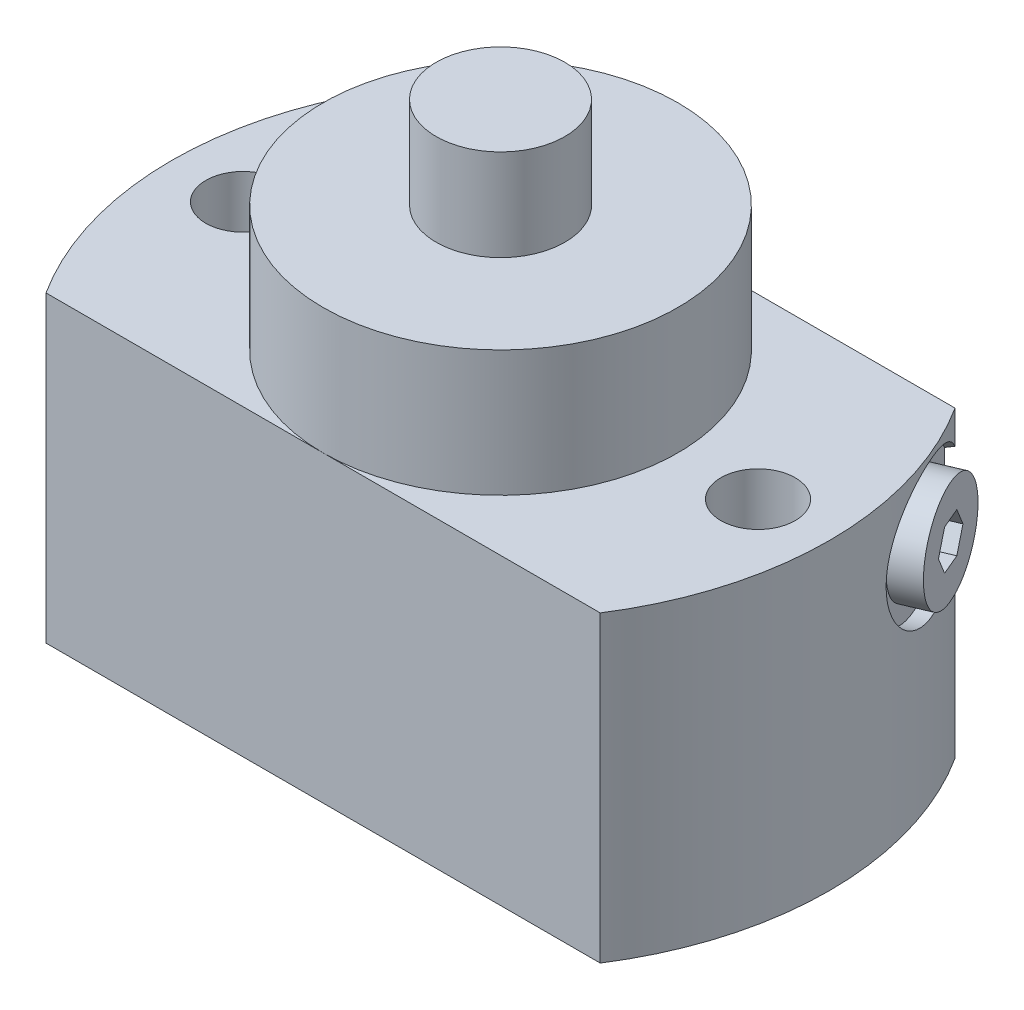
SolidWorks part; units mm, degrees
material "Alloy Steel"
ref_plane "Front Plane" through (0, 0, 0) normal (0, 0, 1) x (1, 0, 0)
ref_plane "Top Plane" through (0, 0, 0) normal (0, 1, 0) x (1, 0, 0)
ref_plane "Right Plane" through (0, 0, 0) normal (1, 0, 0) x (0, 0, -1)
sketch "Sketch1" plane through (0, 0, 0) normal (0, 1, 0) x (1, 0, 0)
  line L0 (-48.4278, 31) -> (48.4278, 31)
  line L1 (0, 0) -> (70.7148, 0) construction
  line L2 (-48.4278, -31) -> (48.4278, -31)
  arc A0 (-48.4278, 31) -> (-48.4278, -31) centre (0, 0) ccw
  arc A1 (48.4278, -31) -> (48.4278, 31) centre (0, 0) ccw
  dimension "D1" = 57.5
  dimension "D2" = 62
extrude "Extrude1" add sketch "Sketch1" along normal blind 53
sketch "Sketch2" plane through (0, 0, 0) normal (0, 0, 1) x (1, 0, 0)
  line L0 (0, 0) -> (0, 90.1953) construction
  line L1 (0, 91) -> (-11.25, 91)
  line L2 (-11.25, 91) -> (-11.25, 75)
  line L3 (-11.25, 75) -> (-31, 75)
  line L6 (-31, 75) -> (-31, 53)
  line L7 (-48.4278, 53) -> (48.4278, 53) construction
  line L8 (-31, 53) -> (0, 53)
  line L9 (0, 53) -> (0, 91)
  line L10 (-48.4278, 0) -> (48.4278, 0) construction
  point P8 (-32.8839, 75)
  dimension "D1" = 22.5
  dimension "D2" = 16
  dimension "D3" = 75
  dimension "D6" = 62
revolve "Revolve1" add sketch "Sketch2" angle 360 about L0
hole_wizard "Hole1" positions "Sketch4" profile "Sketch3" legacy end condition up to next
sketch "Sketch4" plane through (0, 53, 0) normal (0, 1, 0) x (-1, 0, 0)
  line L0 (0, 0) -> (0, 47.5777) construction
  point P0 (45, 0)
  point P7 (-45, 0)
  dimension "D1" = 90
sketch "Sketch3" plane through (-45, 53, 0) normal (1, 0, 0) x (0, 0, 1)
  line L0 (0, 0) -> (0, 53)
  line L1 (0, 53) -> (6.5, 53)
  line L2 (6.5, 53) -> (6.5, 0)
  line L3 (6.5, 0) -> (0, 0)
  line L4 (0, 110) -> (0, -10) construction
  dimension "Diameter" = 13
  dimension "Depth" = 53
sketch "Sketch5" plane through (0, 0, 0) normal (0, -1, 0) x (1, 0, 0)
  circle A0 centre (0, 0) radius 4
  dimension "D1" = 8
extrude "Cut-Extrude1" cut sketch "Sketch5" against normal blind 4
sketch "Sketch6" plane through (0, 0, 0) normal (0, -1, 0) x (1, 0, 0)
  circle A0 centre (35, -15) radius 5.5
  dimension "D3" = 11
  dimension "D1" = 35
  dimension "D2" = 15
extrude "Cut-Extrude2" cut sketch "Sketch6" against normal blind 3
sketch "Sketch7" plane through (0, 3, 0) normal (0, -1, 0) x (1, 0, 0)
  circle A0 centre (35, -15) radius 2
  dimension "D1" = 4
extrude "Cut-Extrude3" cut sketch "Sketch7" against normal blind 33
ref_plane "Plane1" through (0, 0, 0) normal (0.3907, 0, 0.9205) x (0.9205, 0, -0.3907)
sketch "Sketch8" plane through (0, 0, 0) normal (0.3907, 0, 0.9205) x (0.9205, 0, -0.3907)
  line L0 (51.5856, 40) -> (-19.0781, 40) construction
  line L1 (-56.6907, 0) -> (32.4653, 0) construction
  line L2 (57.5, 28) -> (55, 28)
  line L3 (57.5, 0) -> (57.5, 53) construction
  line L4 (55, 28) -> (55, 33.4215)
  line L5 (55, 33.4215) -> (53.5174, 34.2775)
  line L6 (53.5174, 34.2775) -> (35, 34.2775)
  line L7 (35, 34.2775) -> (35, 40)
  line L8 (35, 40) -> (57.5, 40)
  line L9 (57.5, 40) -> (57.5, 28)
  dimension "D1" = 40
  dimension "D2" = 2.5
  dimension "D3" = 20
  dimension "D4" = 11.445
  dimension "D5" = 24
  dimension "D6" = 30
  dimension "D7" = 13.157
revolve "Cut-Revolve1" cut sketch "Sketch8" angle 360 about L0
sketch "Sketch9" plane through (0, 0, 0) normal (0.3907, 0, 0.9205) x (0.9205, 0, -0.3907)
  line L0 (74.5879, 40) -> (15.4121, 40) construction
  line L1 (35, 40) -> (53.5174, 40) construction
  line L2 (55, 28) -> (55, 52) construction
  line L4 (55, 31) -> (55, 34.2775)
  line L5 (46, 34.2775) -> (55, 34.2775)
  line L6 (55, 31) -> (60, 31)
  line L7 (60, 31) -> (60, 40)
  line L8 (60, 40) -> (45, 40)
  line L9 (45, 40) -> (45, 35.2775)
  line L10 (45, 35.2775) -> (46, 34.2775)
  line L12 (40.0743, 34.2775) -> (53.5174, 34.2775) construction
  dimension "D1" = 45
  dimension "D2" = 4.7225
  dimension "D3" = 10
  dimension "D4" = 5
  dimension "D5" = 18
revolve "Revolve2" add sketch "Sketch9" angle 360 about L0
sketch "Sketch10" plane through (55.2303, 0, -23.4439) normal (0.9205, 0, -0.3907) x (-0.3907, 0, -0.9205)
  line L1 (4.0415, 40) -> (2.0207, 43.5)
  line L2 (2.0207, 43.5) -> (-2.0207, 43.5)
  line L3 (-2.0207, 43.5) -> (-4.0415, 40)
  line L4 (-4.0415, 40) -> (-2.0207, 36.5)
  line L5 (-2.0207, 36.5) -> (2.0207, 36.5)
  line L6 (2.0207, 36.5) -> (4.0415, 40)
  circle A0 centre (0, 40) radius 3.5 construction
  circle A1 centre (0, 40) radius 9 construction
  dimension "D1" = 7
extrude "Cut-Extrude4" cut sketch "Sketch10" against normal blind 5
